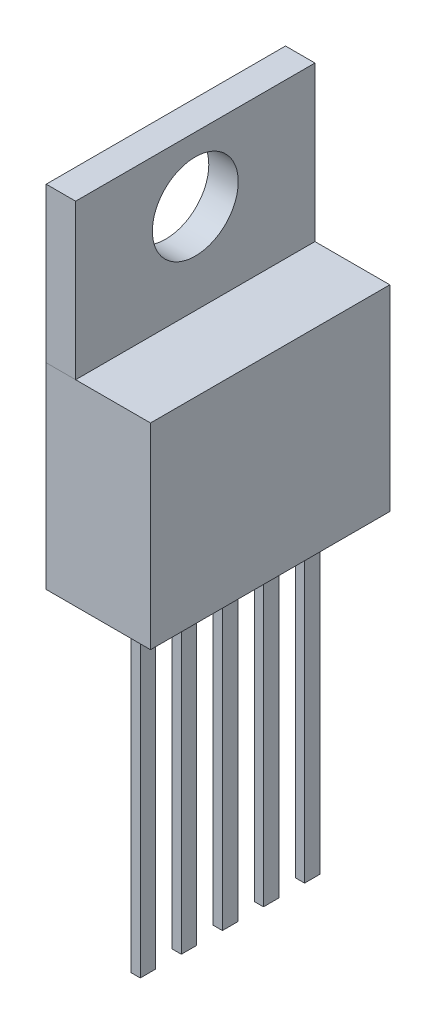
SolidWorks part; units mm, degrees
ref_plane "Front Plane" through (0, 0, 0) normal (0, 0, 1) x (1, 0, 0)
ref_plane "Top Plane" through (0, 0, 0) normal (0, 1, 0) x (1, 0, 0)
ref_plane "Right Plane" through (0, 0, 0) normal (1, 0, 0) x (0, 0, -1)
sketch "Sketch1" plane through (0, 0, 0) normal (1, 0, 0) x (0, 0, -1)
  line L1 (-4.953, 4.064) -> (4.953, 4.064)
  line L2 (-4.953, 4.064) -> (-4.953, -4.064)
  line L3 (-4.953, -4.064) -> (4.953, -4.064)
  line L4 (4.953, 4.064) -> (4.953, -4.064)
  line L5 (-4.953, 4.064) -> (4.953, -4.064) construction
  line L6 (-4.953, -4.064) -> (4.953, 4.064) construction
  point P0 (0, 0)
  dimension "D1" = 8.128
  dimension "D2" = 9.906
extrude "Boss-Extrude1" add sketch "Sketch1" along normal blind 4.318
sketch "Sketch2" plane through (0, 0, 0) normal (1, 0, 0) x (0, 0, -1)
  line L0 (4.953, 4.064) -> (4.953, 10.465)
  line L1 (4.953, 10.465) -> (-4.953, 10.465)
  line L2 (-4.953, 10.465) -> (-4.953, 4.064)
  line L3 (4.953, 4.064) -> (-4.953, 4.064) construction
  line L4 (-4.953, 4.064) -> (4.953, 4.064)
  circle A0 centre (0, 7.798) radius 1.778
  point P0 (0, 10.465)
  point P1 (0, 7.798)
  dimension "D1" = 14.529
  dimension "D2" = 2.667
extrude "Boss-Extrude3" add sketch "Sketch2" along normal blind 1.219
sketch "Sketch3" plane through (0, -4.064, 0) normal (0, -1, 0) x (-1, 0, 0)
  line L0 (-2.591, -1.9493) -> (-2.591, -1.3143)
  line L1 (0, -4.953) -> (0, 4.953) construction
  line L2 (-2.591, -1.3143) -> (-2.21, -1.3143)
  line L3 (-2.21, 0.0682) -> (-2.21, -0.2493)
  line L8 (-2.21, -0.2493) -> (-2.591, -0.2493)
  line L9 (-2.591, -0.2493) -> (-2.591, 0.3857)
  line L10 (-2.591, 0.3857) -> (-2.21, 0.3857)
  line L11 (-2.21, 0.3857) -> (-2.21, 0.0682)
  line L12 (-2.21, -1.6318) -> (-2.21, -1.9493)
  line L13 (-2.21, -1.3143) -> (-2.21, -1.6318)
  line L14 (-2.21, -1.9493) -> (-2.591, -1.9493)
  line L15 (-2.591, -3.6493) -> (-2.591, -3.0143)
  line L16 (-2.591, -3.0143) -> (-2.21, -3.0143)
  line L17 (-2.21, -3.3318) -> (-2.21, -3.6493)
  line L18 (-2.21, -3.0143) -> (-2.21, -3.3318)
  line L19 (-2.21, -3.6493) -> (-2.591, -3.6493)
  line L20 (-2.591, 1.4507) -> (-2.591, 2.0857)
  line L21 (-2.591, 2.0857) -> (-2.21, 2.0857)
  line L22 (-2.21, 1.7682) -> (-2.21, 1.4507)
  line L23 (-2.21, 2.0857) -> (-2.21, 1.7682)
  line L24 (-2.21, 1.4507) -> (-2.591, 1.4507)
  line L25 (-2.591, 3.1507) -> (-2.591, 3.7857)
  line L26 (-2.591, 3.7857) -> (-2.21, 3.7857)
  line L27 (-2.21, 3.4682) -> (-2.21, 3.1507)
  line L28 (-2.21, 3.7857) -> (-2.21, 3.4682)
  line L29 (-2.21, 3.1507) -> (-2.591, 3.1507)
  point P0 (-2.21, 4.1412)
  point P3 (-2.21, 0.0682)
  dimension "D1" = 2.21
  dimension "D2" = 0.3175
  dimension "D3" = 0.3175
  dimension "D4" = 0.381
  dimension "D5" = 0.635
  dimension "D6" = 3
  dimension "D7" = 3
extrude "Boss-Extrude4" add sketch "Sketch3" along normal blind 13.284
sketch "Sketch6" plane through (0, 0, 4.953) normal (0, 0, 1) x (1, 0, 0)
  line L0 (1.219, 4.064) -> (0, 4.064)
  line L1 (0, 10.465) -> (0, -4.064) construction
split line "Split Line1"
sketch "Sketch7" plane through (0, 0, 0) normal (-1, 0, 0) x (0, 0, 1)
  line L0 (4.953, 4.064) -> (-4.953, 4.064)
  line L1 (-4.953, -4.064) -> (-4.953, 10.465) construction
sketch "Sketch8" plane through (0, 0, -4.953) normal (0, 0, -1) x (-1, 0, 0)
  line L0 (0, 4.064) -> (-1.219, 4.064)
split line "Split Line3"
split line "Split Line4"
